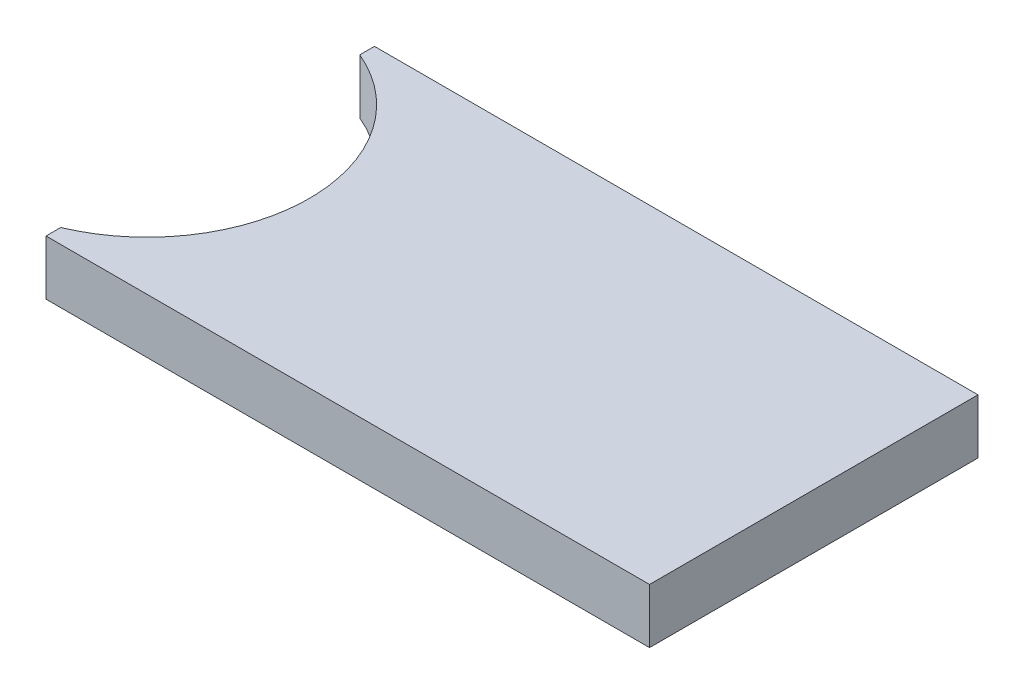
SolidWorks part; units mm, degrees
ref_plane "Спереди" through (0, 0, 0) normal (0, 0, 1) x (1, 0, 0)
ref_plane "Сверху" through (0, 0, 0) normal (0, 1, 0) x (1, 0, 0)
ref_plane "Справа" through (0, 0, 0) normal (1, 0, 0) x (0, 0, -1)
sketch "Эскиз2" plane through (0, 0, 0) normal (0, 1, 0) x (1, 0, 0)
  line L0 (-110.2496, 60) -> (-110.2496, 54.6368)
  line L1 (-110.2496, 60) -> (110.2496, 60)
  line L3 (-110.2496, -60) -> (110.2496, -60)
  line L4 (110.2496, 60) -> (110.2496, -60)
  line L5 (-110.2496, 60) -> (110.2496, -60) construction
  line L6 (-110.2496, -60) -> (110.2496, 60) construction
  line L7 (-110.2496, -60) -> (-110.2496, -54.6368)
  line L8 (-133.3374, 0) -> (121.3538, 0) construction
  arc A1 (-110.2496, 54.6368) -> (-110.2496, -54.6368) centre (-133.3374, 0) cw
  point P0 (0, 0)
  point P7 (-134.9724, 0)
  point P12 (0, 0)
extrude "Бобышка-Вытянуть1" add sketch "Эскиз2" along normal blind 20
